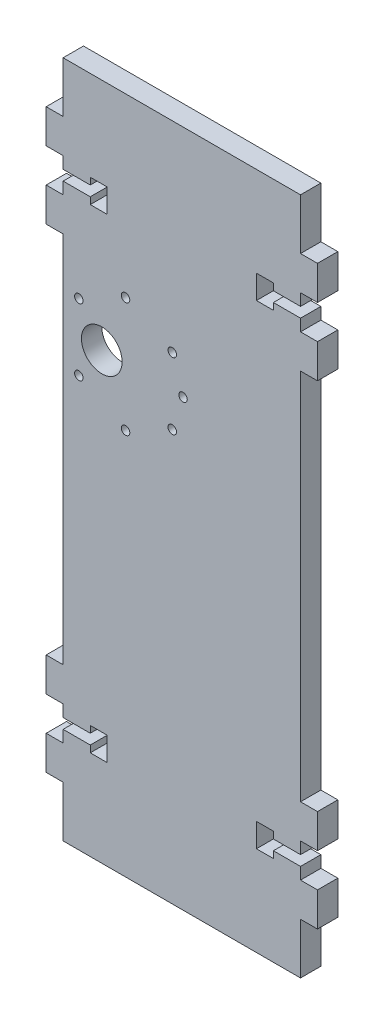
SolidWorks part; units mm, degrees
material "Cedro"
ref_plane "Plano frontal" through (0, 0, 0) normal (0, 0, 1) x (1, 0, 0)
ref_plane "Plano superior" through (0, 0, 0) normal (0, 1, 0) x (1, 0, 0)
ref_plane "Plano direito" through (0, 0, 0) normal (1, 0, 0) x (0, 0, -1)
sketch "Model" plane through (0, 0, 0) normal (0, 0, 1) x (1, 0, 0)
  line L0 (70, -31.5) -> (62, -31.5)
  line L1 (62, -31.5) -> (62, -33.5)
  line L2 (62, -33.5) -> (57, -33.5)
  line L3 (57, -33.5) -> (57, -26.5)
  line L4 (57, -26.5) -> (62, -26.5)
  line L5 (62, -26.5) -> (62, -28.5)
  line L6 (62, -28.5) -> (70, -28.5)
  line L7 (70, -28.5) -> (70, -25)
  line L8 (70, -25) -> (75, -25)
  line L9 (75, -25) -> (75, -15)
  line L10 (75, -15) -> (70, -15)
  line L11 (70, -15) -> (70, 0)
  line L12 (70, 0) -> (0, 0)
  line L13 (0, 0) -> (0, -15)
  line L14 (0, -15) -> (-5, -15)
  line L15 (-5, -15) -> (-5, -25)
  line L16 (-5, -25) -> (0, -25)
  line L17 (0, -25) -> (0, -28.5)
  line L18 (0, -28.5) -> (8, -28.5)
  line L19 (8, -28.5) -> (8, -26.5)
  line L20 (8, -26.5) -> (13, -26.5)
  line L21 (13, -26.5) -> (13, -33.5)
  line L22 (13, -33.5) -> (8, -33.5)
  line L23 (8, -33.5) -> (8, -31.5)
  line L24 (8, -31.5) -> (0, -31.5)
  line L25 (0, -31.5) -> (0, -35)
  line L26 (0, -35) -> (-5, -35)
  line L27 (-5, -35) -> (-5, -45)
  line L28 (-5, -45) -> (0, -45)
  line L29 (0, -45) -> (0, -155)
  line L30 (0, -155) -> (-5, -155)
  line L31 (-5, -155) -> (-5, -165)
  line L32 (-5, -165) -> (0, -165)
  line L33 (0, -165) -> (0, -168.5)
  line L34 (0, -168.5) -> (8, -168.5)
  line L35 (8, -168.5) -> (8, -166.5)
  line L36 (8, -166.5) -> (13, -166.5)
  line L37 (13, -166.5) -> (13, -173.5)
  line L38 (13, -173.5) -> (8, -173.5)
  line L39 (8, -173.5) -> (8, -171.5)
  line L40 (8, -171.5) -> (0, -171.5)
  line L41 (0, -171.5) -> (0, -175)
  line L42 (0, -175) -> (-5, -175)
  line L43 (-5, -175) -> (-5, -185)
  line L44 (-5, -185) -> (0, -185)
  line L45 (0, -185) -> (0, -200)
  line L46 (0, -200) -> (70, -200)
  line L47 (70, -200) -> (70, -185)
  line L48 (70, -185) -> (75, -185)
  line L49 (75, -185) -> (75, -175)
  line L50 (75, -175) -> (70, -175)
  line L51 (70, -175) -> (70, -171.5)
  line L52 (70, -171.5) -> (62, -171.5)
  line L53 (62, -171.5) -> (62, -173.5)
  line L54 (62, -173.5) -> (57, -173.5)
  line L55 (57, -173.5) -> (57, -166.5)
  line L56 (57, -166.5) -> (62, -166.5)
  line L57 (62, -166.5) -> (62, -168.5)
  line L58 (62, -168.5) -> (70, -168.5)
  line L59 (70, -168.5) -> (70, -165)
  line L60 (70, -165) -> (75, -165)
  line L61 (75, -165) -> (75, -155)
  line L62 (75, -155) -> (70, -155)
  line L63 (70, -155) -> (70, -45)
  line L64 (70, -45) -> (75, -45)
  line L65 (75, -45) -> (75, -35)
  line L66 (75, -35) -> (70, -35)
  line L67 (70, -35) -> (70, -31.5)
  circle A0 centre (32.177, -78.842) radius 1.25
  circle A1 centre (35.353, -69) radius 1.25
  circle A2 centre (32.177, -59.158) radius 1.25
  circle A3 centre (18.403, -52.05) radius 1.25
  circle A4 centre (4.629, -59.158) radius 1.25
  circle A5 centre (4.629, -78.842) radius 1.25
  circle A6 centre (18.403, -85.95) radius 1.25
  circle A7 centre (11.4, -69) radius 6
extrude "Ressalto-extrusão1" add sketch "Model" along normal blind 6
